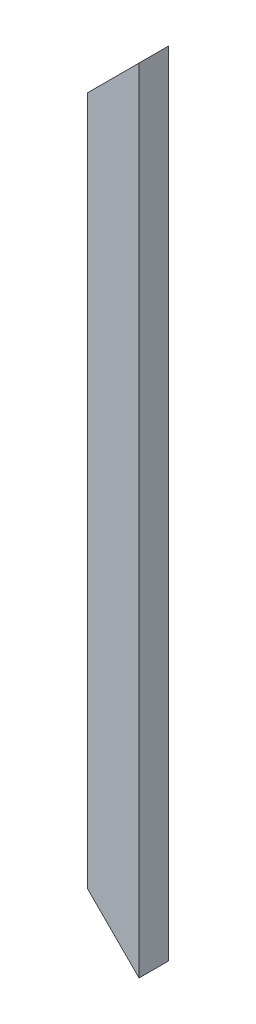
SolidWorks part; units mm, degrees
ref_plane "Front Plane" through (0, 0, 0) normal (0, 0, 1) x (1, 0, 0)
ref_plane "Top Plane" through (0, 0, 0) normal (0, 1, 0) x (1, 0, 0)
ref_plane "Right Plane" through (0, 0, 0) normal (1, 0, 0) x (0, 0, -1)
sketch "Sketch1" plane through (0, 0, 0) normal (1, 0, 0) x (0, 0, -1)
  line L1 (0, 0) -> (25.4, 0)
  line L2 (0, 0) -> (0, 682.4995)
  line L3 (0, 682.4995) -> (25.4, 682.4995)
  line L4 (25.4, 0) -> (25.4, 682.4995)
  dimension "D1" = 682.4995
  dimension "D2" = 25.4
extrude "Boss-Extrude1" add sketch "Sketch1" along normal blind 44.45
sketch "Sketch2" plane through (0, 0, 0) normal (0, 0, 1) x (1, 0, 0)
  line L0 (44.45, 0) -> (0, 44.45)
  line L1 (0, 682.4995) -> (0, 0) construction
  line L4 (0, 44.45) -> (0, 0)
  line L5 (0, 0) -> (44.45, 0)
  dimension "D1" = 45
extrude "Cut-Extrude1" cut sketch "Sketch2" against normal blind 44.45
sketch "Sketch3" plane through (0, 0, 0) normal (0, 0, 1) x (1, 0, 0)
  line L0 (0, 638.0495) -> (44.45, 682.4995)
  line L1 (0, 682.4995) -> (0, 44.45) construction
  line L2 (44.45, 682.4995) -> (0, 682.4995)
  line L3 (44.45, 682.4995) -> (0, 682.4995) construction
  line L4 (0, 682.4995) -> (0, 638.0495)
  dimension "D1" = 45
extrude "Cut-Extrude2" cut sketch "Sketch3" against normal blind 44.45
